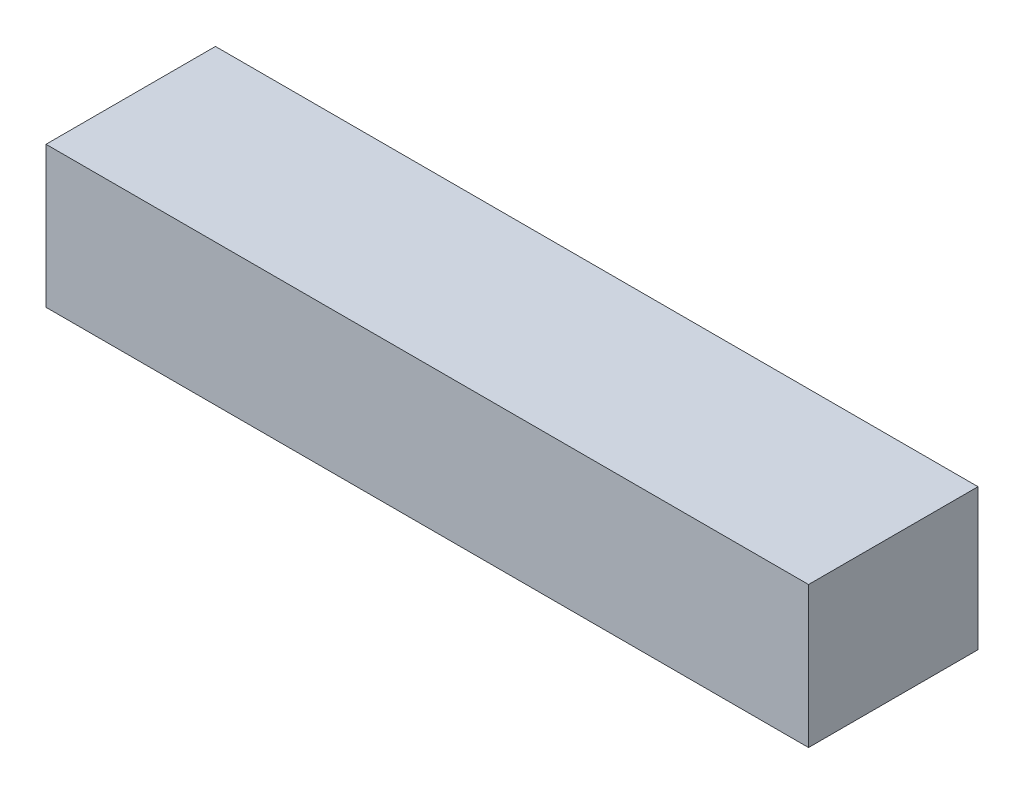
SolidWorks part; units mm, degrees
ref_plane "正面" through (0, 0, 0) normal (0, 0, 1) x (1, 0, 0)
ref_plane "平面" through (0, 0, 0) normal (0, 1, 0) x (1, 0, 0)
ref_plane "右側面" through (0, 0, 0) normal (1, 0, 0) x (0, 0, -1)
sketch "ｽｹｯﾁ1" plane through (0, 0, 0) normal (0, 1, 0) x (1, 0, 0)
  line L1 (0, 0) -> (27, 0)
  line L2 (0, 0) -> (0, -6)
  line L3 (0, -6) -> (27, -6)
  line L4 (27, 0) -> (27, -6)
  dimension "D1" = 6
  dimension "D2" = 27
extrude "ﾎﾞｽ - 押し出し1" add sketch "ｽｹｯﾁ1" along normal blind 5
